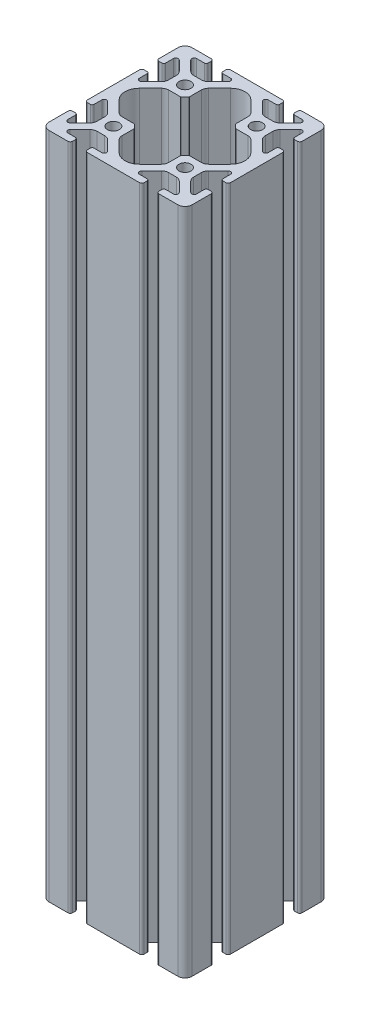
SolidWorks part; units mm, degrees
ref_plane "Piano frontale" through (0, 0, 0) normal (0, 0, 1) x (1, 0, 0)
ref_plane "Piano superiore" through (0, 0, 0) normal (0, 1, 0) x (1, 0, 0)
ref_plane "Piano destro" through (0, 0, 0) normal (1, 0, 0) x (0, 0, -1)
ref_plane "Piano1" through (0, -10, 0) normal (0, -1, 0) x (1, 0, 0)
sketch "Schizzo1" plane through (0, -10, 0) normal (0, -1, 0) x (1, 0, 0)
  line L0 (-4.2426, -23.3532) -> (-8.8713, -18.7245)
  line L1 (-9.75, -16.6032) -> (-9.75, -11.6703)
  line L2 (-9.8964, -11.3168) -> (-11.3168, -9.8964)
  line L3 (-11.6703, -9.75) -> (-16.6032, -9.75)
  line L4 (-18.7245, -8.8713) -> (-23.3532, -4.2426)
  line L5 (-23.3532, 4.2426) -> (-18.7245, 8.8713)
  line L6 (-16.6032, 9.75) -> (-11.6703, 9.75)
  line L7 (-11.3168, 9.8964) -> (-9.8964, 11.3168)
  line L8 (-9.75, 11.6703) -> (-9.75, 16.6032)
  line L9 (-8.8713, 18.7245) -> (-4.2426, 23.3532)
  line L10 (4.2426, 23.3532) -> (8.8713, 18.7245)
  line L11 (9.75, 16.6032) -> (9.75, 11.6703)
  line L12 (9.8964, 11.3168) -> (11.3168, 9.8964)
  line L13 (11.6703, 9.75) -> (16.6032, 9.75)
  line L14 (18.7245, 8.8713) -> (23.3532, 4.2426)
  line L15 (23.3532, -4.2426) -> (18.7245, -8.8713)
  line L16 (16.6032, -9.75) -> (11.6703, -9.75)
  line L17 (11.3168, -9.8964) -> (9.8964, -11.3168)
  line L18 (9.75, -11.6703) -> (9.75, -16.6032)
  line L19 (8.8713, -18.7245) -> (4.2426, -23.3532)
  line L20 (11.9, 27.8) -> (11.9, 29)
  line L21 (10.9, 30) -> (-10.9, 30)
  line L22 (-11.9, 29) -> (-11.9, 27.8)
  line L23 (-11.1, 27) -> (-7.8724, 27)
  line L24 (-7.1494, 25.2547) -> (-11.2755, 21.1287)
  line L25 (-13.3968, 20.25) -> (-16.6032, 20.25)
  line L26 (-18.7245, 21.1287) -> (-22.8506, 25.2547)
  line L27 (-22.1276, 27) -> (-18.9, 27)
  line L28 (-18.1, 27.8) -> (-18.1, 29)
  line L29 (-19.1, 30) -> (-27, 30)
  line L30 (-30, 27) -> (-30, 19.1)
  line L31 (-29, 18.1) -> (-27.8, 18.1)
  line L32 (-27, 18.9) -> (-27, 22.1276)
  line L33 (-25.2547, 22.8506) -> (-21.1287, 18.7245)
  line L34 (-20.25, 16.6032) -> (-20.25, 13.3968)
  line L35 (-21.1287, 11.2755) -> (-25.2547, 7.1494)
  line L36 (-27, 7.8724) -> (-27, 11.1)
  line L37 (-27.8, 11.9) -> (-29, 11.9)
  line L38 (-30, 10.9) -> (-30, -10.9)
  line L39 (-29, -11.9) -> (-27.8, -11.9)
  line L40 (-27, -11.1) -> (-27, -7.8724)
  line L41 (-25.2547, -7.1494) -> (-21.1287, -11.2755)
  line L42 (-20.25, -13.3968) -> (-20.25, -16.6032)
  line L43 (-21.1287, -18.7245) -> (-25.2547, -22.8506)
  line L44 (-27, -22.1276) -> (-27, -18.9)
  line L45 (-27.8, -18.1) -> (-29, -18.1)
  line L46 (-30, -19.1) -> (-30, -27)
  line L47 (-27, -30) -> (-19.1, -30)
  line L48 (-18.1, -29) -> (-18.1, -27.8)
  line L49 (-18.9, -27) -> (-22.1276, -27)
  line L50 (-22.8506, -25.2547) -> (-18.7245, -21.1287)
  line L51 (-16.6032, -20.25) -> (-13.3968, -20.25)
  line L52 (-11.2755, -21.1287) -> (-7.1494, -25.2547)
  line L53 (-7.8724, -27) -> (-11.1, -27)
  line L54 (-11.9, -27.8) -> (-11.9, -29)
  line L55 (-10.9, -30) -> (10.9, -30)
  line L56 (11.9, -29) -> (11.9, -27.8)
  line L57 (11.1, -27) -> (7.8724, -27)
  line L58 (7.1494, -25.2547) -> (11.2755, -21.1287)
  line L59 (13.3968, -20.25) -> (16.6032, -20.25)
  line L60 (18.7245, -21.1287) -> (22.8506, -25.2547)
  line L61 (22.1276, -27) -> (18.9, -27)
  line L62 (18.1, -27.8) -> (18.1, -29)
  line L63 (19.1, -30) -> (27, -30)
  line L64 (30, -27) -> (30, -19.1)
  line L65 (29, -18.1) -> (27.8, -18.1)
  line L66 (27, -18.9) -> (27, -22.1276)
  line L67 (25.2547, -22.8506) -> (21.1287, -18.7245)
  line L68 (20.25, -16.6032) -> (20.25, -13.3968)
  line L69 (21.1287, -11.2755) -> (25.2547, -7.1494)
  line L70 (27, -7.8724) -> (27, -11.1)
  line L71 (27.8, -11.9) -> (29, -11.9)
  line L72 (30, -10.9) -> (30, 10.9)
  line L73 (29, 11.9) -> (27.8, 11.9)
  line L74 (27, 11.1) -> (27, 7.8724)
  line L75 (25.2547, 7.1494) -> (21.1287, 11.2755)
  line L76 (20.25, 13.3968) -> (20.25, 16.6032)
  line L77 (21.1287, 18.7245) -> (25.2547, 22.8506)
  line L78 (27, 22.1276) -> (27, 18.9)
  line L79 (27.8, 18.1) -> (29, 18.1)
  line L80 (30, 19.1) -> (30, 27)
  line L81 (27, 30) -> (19.1, 30)
  line L82 (18.1, 29) -> (18.1, 27.8)
  line L83 (18.9, 27) -> (22.1276, 27)
  line L84 (22.8506, 25.2547) -> (18.7245, 21.1287)
  line L85 (16.6032, 20.25) -> (13.3968, 20.25)
  line L86 (11.2755, 21.1287) -> (7.1494, 25.2547)
  line L87 (7.8724, 27) -> (11.1, 27)
  circle A0 centre (-15, -15) radius 2.5
  circle A1 centre (15, -15) radius 2.5
  circle A2 centre (15, 15) radius 2.5
  circle A3 centre (-15, 15) radius 2.5
  arc A4 (-8.8713, -18.7245) -> (-9.75, -16.6032) centre (-6.75, -16.6032) cw
  arc A5 (-9.75, -11.6703) -> (-9.8964, -11.3168) centre (-10.25, -11.6703) ccw
  arc A6 (-11.3168, -9.8964) -> (-11.6703, -9.75) centre (-11.6703, -10.25) ccw
  arc A7 (-16.6032, -9.75) -> (-18.7245, -8.8713) centre (-16.6032, -6.75) cw
  arc A8 (-23.3532, -4.2426) -> (-23.3532, 4.2426) centre (-19.1106, 0) cw
  arc A9 (-18.7245, 8.8713) -> (-16.6032, 9.75) centre (-16.6032, 6.75) cw
  arc A10 (-11.6703, 9.75) -> (-11.3168, 9.8964) centre (-11.6703, 10.25) ccw
  arc A11 (-9.8964, 11.3168) -> (-9.75, 11.6703) centre (-10.25, 11.6703) ccw
  arc A12 (-9.75, 16.6032) -> (-8.8713, 18.7245) centre (-6.75, 16.6032) cw
  arc A13 (-4.2426, 23.3532) -> (4.2426, 23.3532) centre (0, 19.1106) cw
  arc A14 (8.8713, 18.7245) -> (9.75, 16.6032) centre (6.75, 16.6032) cw
  arc A15 (9.75, 11.6703) -> (9.8964, 11.3168) centre (10.25, 11.6703) ccw
  arc A16 (11.3168, 9.8964) -> (11.6703, 9.75) centre (11.6703, 10.25) ccw
  arc A17 (16.6032, 9.75) -> (18.7245, 8.8713) centre (16.6032, 6.75) cw
  arc A18 (23.3532, 4.2426) -> (23.3532, -4.2426) centre (19.1106, 0) cw
  arc A19 (18.7245, -8.8713) -> (16.6032, -9.75) centre (16.6032, -6.75) cw
  arc A20 (11.6703, -9.75) -> (11.3168, -9.8964) centre (11.6703, -10.25) ccw
  arc A21 (9.8964, -11.3168) -> (9.75, -11.6703) centre (10.25, -11.6703) ccw
  arc A22 (9.75, -16.6032) -> (8.8713, -18.7245) centre (6.75, -16.6032) cw
  arc A23 (4.2426, -23.3532) -> (-4.2426, -23.3532) centre (0, -19.1106) cw
  arc A24 (11.1, 27) -> (11.9, 27.8) centre (11.1, 27.8) ccw
  arc A25 (11.9, 29) -> (10.9, 30) centre (10.9, 29) ccw
  arc A26 (-10.9, 30) -> (-11.9, 29) centre (-10.9, 29) ccw
  arc A27 (-11.9, 27.8) -> (-11.1, 27) centre (-11.1, 27.8) ccw
  arc A28 (-7.8724, 27) -> (-7.1494, 25.2547) centre (-7.8724, 25.9776) cw
  arc A29 (-11.2755, 21.1287) -> (-13.3968, 20.25) centre (-13.3968, 23.25) cw
  arc A30 (-16.6032, 20.25) -> (-18.7245, 21.1287) centre (-16.6032, 23.25) cw
  arc A31 (-22.8506, 25.2547) -> (-22.1276, 27) centre (-22.1276, 25.9776) cw
  arc A32 (-18.9, 27) -> (-18.1, 27.8) centre (-18.9, 27.8) ccw
  arc A33 (-18.1, 29) -> (-19.1, 30) centre (-19.1, 29) ccw
  arc A34 (-27, 30) -> (-30, 27) centre (-27, 27) ccw
  arc A35 (-30, 19.1) -> (-29, 18.1) centre (-29, 19.1) ccw
  arc A36 (-27.8, 18.1) -> (-27, 18.9) centre (-27.8, 18.9) ccw
  arc A37 (-27, 22.1276) -> (-25.2547, 22.8506) centre (-25.9776, 22.1276) cw
  arc A38 (-21.1287, 18.7245) -> (-20.25, 16.6032) centre (-23.25, 16.6032) cw
  arc A39 (-20.25, 13.3968) -> (-21.1287, 11.2755) centre (-23.25, 13.3968) cw
  arc A40 (-25.2547, 7.1494) -> (-27, 7.8724) centre (-25.9776, 7.8724) cw
  arc A41 (-27, 11.1) -> (-27.8, 11.9) centre (-27.8, 11.1) ccw
  arc A42 (-29, 11.9) -> (-30, 10.9) centre (-29, 10.9) ccw
  arc A43 (-30, -10.9) -> (-29, -11.9) centre (-29, -10.9) ccw
  arc A44 (-27.8, -11.9) -> (-27, -11.1) centre (-27.8, -11.1) ccw
  arc A45 (-27, -7.8724) -> (-25.2547, -7.1494) centre (-25.9776, -7.8724) cw
  arc A46 (-21.1287, -11.2755) -> (-20.25, -13.3968) centre (-23.25, -13.3968) cw
  arc A47 (-20.25, -16.6032) -> (-21.1287, -18.7245) centre (-23.25, -16.6032) cw
  arc A48 (-25.2547, -22.8506) -> (-27, -22.1276) centre (-25.9776, -22.1276) cw
  arc A49 (-27, -18.9) -> (-27.8, -18.1) centre (-27.8, -18.9) ccw
  arc A50 (-29, -18.1) -> (-30, -19.1) centre (-29, -19.1) ccw
  arc A51 (-30, -27) -> (-27, -30) centre (-27, -27) ccw
  arc A52 (-19.1, -30) -> (-18.1, -29) centre (-19.1, -29) ccw
  arc A53 (-18.1, -27.8) -> (-18.9, -27) centre (-18.9, -27.8) ccw
  arc A54 (-22.1276, -27) -> (-22.8506, -25.2547) centre (-22.1276, -25.9776) cw
  arc A55 (-18.7245, -21.1287) -> (-16.6032, -20.25) centre (-16.6032, -23.25) cw
  arc A56 (-13.3968, -20.25) -> (-11.2755, -21.1287) centre (-13.3968, -23.25) cw
  arc A57 (-7.1494, -25.2547) -> (-7.8724, -27) centre (-7.8724, -25.9776) cw
  arc A58 (-11.1, -27) -> (-11.9, -27.8) centre (-11.1, -27.8) ccw
  arc A59 (-11.9, -29) -> (-10.9, -30) centre (-10.9, -29) ccw
  arc A60 (10.9, -30) -> (11.9, -29) centre (10.9, -29) ccw
  arc A61 (11.9, -27.8) -> (11.1, -27) centre (11.1, -27.8) ccw
  arc A62 (7.8724, -27) -> (7.1494, -25.2547) centre (7.8724, -25.9776) cw
  arc A63 (11.2755, -21.1287) -> (13.3968, -20.25) centre (13.3968, -23.25) cw
  arc A64 (16.6032, -20.25) -> (18.7245, -21.1287) centre (16.6032, -23.25) cw
  arc A65 (22.8506, -25.2547) -> (22.1276, -27) centre (22.1276, -25.9776) cw
  arc A66 (18.9, -27) -> (18.1, -27.8) centre (18.9, -27.8) ccw
  arc A67 (18.1, -29) -> (19.1, -30) centre (19.1, -29) ccw
  arc A68 (27, -30) -> (30, -27) centre (27, -27) ccw
  arc A69 (30, -19.1) -> (29, -18.1) centre (29, -19.1) ccw
  arc A70 (27.8, -18.1) -> (27, -18.9) centre (27.8, -18.9) ccw
  arc A71 (27, -22.1276) -> (25.2547, -22.8506) centre (25.9776, -22.1276) cw
  arc A72 (21.1287, -18.7245) -> (20.25, -16.6032) centre (23.25, -16.6032) cw
  arc A73 (20.25, -13.3968) -> (21.1287, -11.2755) centre (23.25, -13.3968) cw
  arc A74 (25.2547, -7.1494) -> (27, -7.8724) centre (25.9776, -7.8724) cw
  arc A75 (27, -11.1) -> (27.8, -11.9) centre (27.8, -11.1) ccw
  arc A76 (29, -11.9) -> (30, -10.9) centre (29, -10.9) ccw
  arc A77 (30, 10.9) -> (29, 11.9) centre (29, 10.9) ccw
  arc A78 (27.8, 11.9) -> (27, 11.1) centre (27.8, 11.1) ccw
  arc A79 (27, 7.8724) -> (25.2547, 7.1494) centre (25.9776, 7.8724) cw
  arc A80 (21.1287, 11.2755) -> (20.25, 13.3968) centre (23.25, 13.3968) cw
  arc A81 (20.25, 16.6032) -> (21.1287, 18.7245) centre (23.25, 16.6032) cw
  arc A82 (25.2547, 22.8506) -> (27, 22.1276) centre (25.9776, 22.1276) cw
  arc A83 (27, 18.9) -> (27.8, 18.1) centre (27.8, 18.9) ccw
  arc A84 (29, 18.1) -> (30, 19.1) centre (29, 19.1) ccw
  arc A85 (30, 27) -> (27, 30) centre (27, 27) ccw
  arc A86 (19.1, 30) -> (18.1, 29) centre (19.1, 29) ccw
  arc A87 (18.1, 27.8) -> (18.9, 27) centre (18.9, 27.8) ccw
  arc A88 (22.1276, 27) -> (22.8506, 25.2547) centre (22.1276, 25.9776) cw
  arc A89 (18.7245, 21.1287) -> (16.6032, 20.25) centre (16.6032, 23.25) cw
  arc A90 (13.3968, 20.25) -> (11.2755, 21.1287) centre (13.3968, 23.25) cw
  arc A91 (7.1494, 25.2547) -> (7.8724, 27) centre (7.8724, 25.9776) cw
extrude "Estrusione-Estrusione1" add sketch "Schizzo1" against normal blind 280
